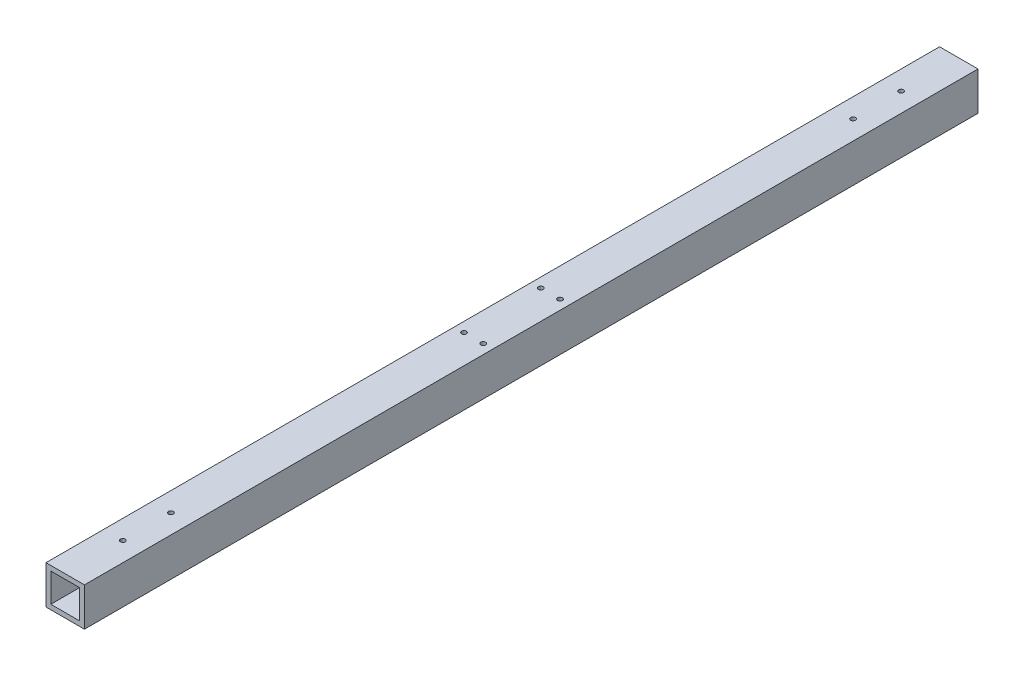
SolidWorks part; units mm, degrees
ref_plane "Front Plane" through (0, 0, 0) normal (0, 0, 1) x (1, 0, 0)
ref_plane "Top Plane" through (0, 0, 0) normal (0, 1, 0) x (1, 0, 0)
ref_plane "Right Plane" through (0, 0, 0) normal (1, 0, 0) x (0, 0, -1)
sketch "Sketch1" plane through (0, 0, 0) normal (0, 0, 1) x (1, 0, 0)
  line L1 (25.4, 25.4) -> (-25.4, 25.4)
  line L2 (25.4, 25.4) -> (25.4, -25.4)
  line L3 (25.4, -25.4) -> (-25.4, -25.4)
  line L4 (-25.4, 25.4) -> (-25.4, -25.4)
  line L5 (25.4, 25.4) -> (-25.4, -25.4) construction
  line L6 (25.4, -25.4) -> (-25.4, 25.4) construction
  point P0 (0, 0)
  dimension "D1" = 50.8
  dimension "D2" = 50.8
extrude "Boss-Extrude1" add sketch "Sketch1" along normal blind 1181.1 contours L1 L4 L3 L2
ref_plane "Plane1" through (0, 0, 0) normal (1, 0, 0) x (0, 0, -1)
ref_plane "Plane2" through (0, 0, 590.55) normal (0, 0, 1) x (1, 0, 0)
ref_point "Point1"
sketch "Sketch8" plane through (0, 0, 1181.1) normal (0, 0, 1) x (1, 0, 0)
  line L0 (-25.4, 25.4) -> (-25.4, -25.4) construction
  line L1 (19.05, -19.05) -> (-19.05, -19.05)
  line L2 (19.05, -19.05) -> (19.05, 19.05)
  line L3 (19.05, 19.05) -> (-19.05, 19.05)
  line L4 (-19.05, -19.05) -> (-19.05, 19.05)
  line L5 (19.05, -19.05) -> (-19.05, 19.05) construction
  line L6 (19.05, 19.05) -> (-19.05, -19.05) construction
  line L7 (25.4, 25.4) -> (-25.4, 25.4) construction
  point P0 (0, 0)
  dimension "D1" = 6.35
  dimension "D2" = 6.35
extrude "Cut-Extrude1" cut sketch "Sketch8" against normal through all
hole_wizard "1/4 (0.25) Diameter Hole1" positions "Sketch4" profile "Sketch5" hole size "1/4" standard "ANSI Inch" end condition through all
sketch "Sketch4" plane through (0, 25.4, 0) normal (0, 1, 0) x (1, 0, 0)
  line L0 (-27.94, -590.55) -> (27.94, -590.55) construction
  line L1 (0, -27.94) -> (0, 27.94) construction
  point P0 (-12.7, -641.35)
  point P7 (12.7, -641.35)
  point P8 (12.7, -539.75)
  point P9 (-12.7, -539.75)
  dimension "D1" = 50.8
  dimension "D2" = 12.7
sketch "Sketch5" plane through (-12.7, 25.4, 641.35) normal (1, 0, 0) x (0, 0, 1)
  line L0 (0, 0) -> (0, 50.8)
  line L1 (0, 50.8) -> (3.175, 50.8)
  line L2 (3.175, 50.8) -> (3.175, 0)
  line L5 (3.175, 0) -> (0, 0)
  line L11 (0, -6.35) -> (0, 107.95) construction
  dimension "Thru Hole Dia." = 6.35
  dimension "Thru Hole Depth" = 50.8
hole_wizard "E (0.25) Diameter Hole2" positions "Sketch9" profile "Sketch10" hole size "E" standard "ANSI Inch" end condition through all
sketch "Sketch9" plane through (0, 25.4, 0) normal (0, 1, 0) x (1, 0, 0)
  line L0 (25.4, -1181.1) -> (-25.4, -1181.1) construction
  line L1 (-27.94, -590.55) -> (27.94, -590.55) construction
  point P0 (0, -1104.9)
  point P2 (0, -1041.4)
  point P9 (0, -139.7)
  point P10 (0, -76.2)
  dimension "D1" = 63.5
  dimension "D2" = 76.2
sketch "Sketch10" plane through (0, 25.4, 1104.9) normal (1, 0, 0) x (0, 0, 1)
  line L0 (0, 0) -> (0, 50.8)
  line L1 (0, 50.8) -> (3.175, 50.8)
  line L2 (3.175, 50.8) -> (3.175, 0)
  line L5 (3.175, 0) -> (0, 0)
  line L11 (0, -6.35) -> (0, 107.95) construction
  dimension "Thru Hole Dia." = 6.35
  dimension "Thru Hole Depth" = 50.8
